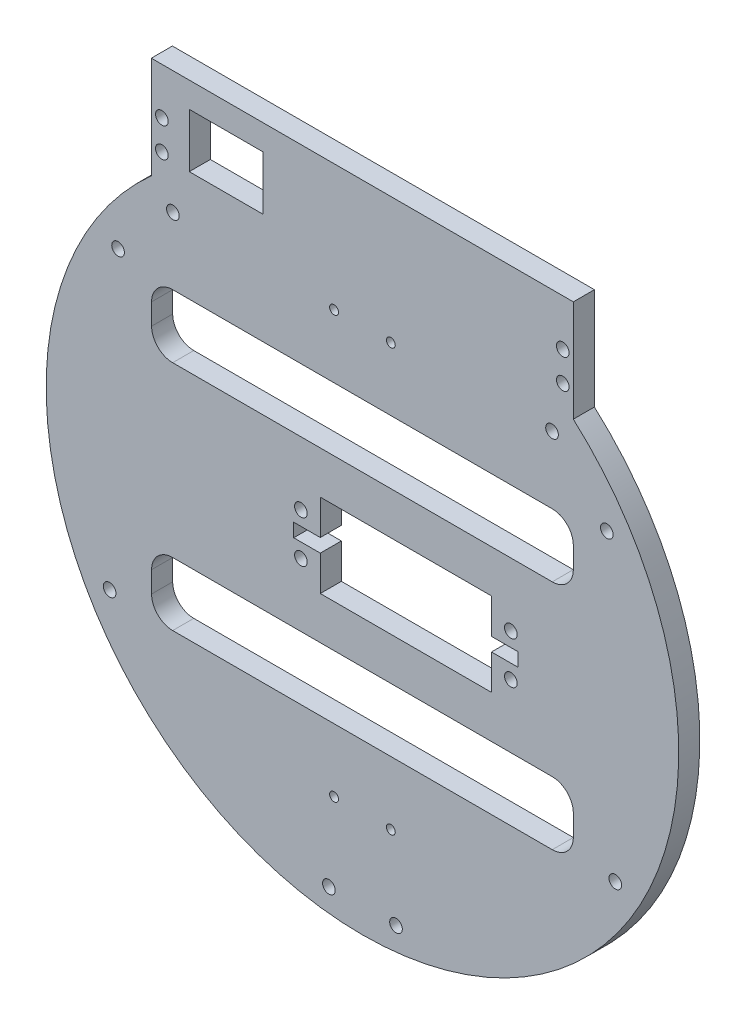
SolidWorks part; units mm, degrees
material "Acrílico (médio-alto impacto)"
ref_plane "Plano frontal" through (0, 0, 0) normal (0, 0, 1) x (1, 0, 0)
ref_plane "Plano superior" through (0, 0, 0) normal (0, 1, 0) x (1, 0, 0)
ref_plane "Plano direito" through (0, 0, 0) normal (1, 0, 0) x (0, 0, -1)
sketch "Esboço1" plane through (0, 0, 0) normal (0, 0, 1) x (1, 0, 0)
  line L0 (44.4954, -168.4305) -> (22.4463, -168.4305) construction
  line L1 (-33.4554, -168.4305) -> (-55.5046, -168.4305) construction
  line L2 (44.4954, -168.4305) -> (44.4954, -144.3322)
  line L3 (-55.5734, -168.3931) -> (-55.5734, -144.3322)
  line L4 (-55.5734, -144.3322) -> (44.4954, -144.3322)
  line L10 (-55.5046, -168.4305) -> (-55.5734, -168.3931)
  arc A0 (-55.5046, -168.4305) -> (44.4954, -168.4305) centre (-5.5046, -224.3322) ccw
  arc A1 (-33.4554, -168.4305) -> (22.4463, -168.4305) centre (-5.5046, -224.3322) ccw construction
  dimension "D1" = 150
  dimension "D2" = 125
  dimension "D3" = 80
extrude "Ressalto-extrusão1" add sketch "Esboço1" along normal blind 5 contours A0 L2 L4 L3 L10
sketch "Esboço2" plane through (0, 0, 5) normal (0, 0, 1) x (1, 0, 0)
  line L1 (-5.5046, -299.3322) -> (-5.5046, -271.3491) construction
  circle A0 centre (39.4463, -173.4305) radius 1.5
  circle A1 centre (52.4463, -187.4305) radius 1.5
  circle A2 centre (54.4463, -258.4305) radius 1.5
  circle A3 centre (-13.4554, -293.4305) radius 1.5
  circle A4 centre (2.4463, -293.4305) radius 1.5
  circle A5 centre (-65.4554, -258.4305) radius 1.5
  circle A8 centre (-63.4554, -187.4305) radius 1.5
  circle A9 centre (-50.4554, -173.4305) radius 1.5
  dimension "D3" = 3
  dimension "D6" = 3
  dimension "D9" = 3
  dimension "D12" = 3
extrude "Corte-extrusão1" cut sketch "Esboço2" against normal blind 10
sketch "Esboço3" plane through (0, 0, 5) normal (0, 0, 1) x (1, 0, 0)
  line L0 (-15.5046, -222.7322) -> (-15.5046, -214.4322)
  line L1 (-15.5046, -234.2322) -> (25.0954, -234.2322)
  line L2 (-15.5046, -234.2322) -> (-15.5046, -225.9322)
  line L3 (-15.5046, -214.4322) -> (25.0954, -214.4322)
  line L4 (25.0954, -234.2322) -> (25.0954, -214.4322)
  line L5 (25.0954, -225.9322) -> (31.3954, -225.9322)
  line L6 (25.0954, -225.9322) -> (25.0954, -222.7322)
  line L7 (25.0954, -222.7322) -> (31.3954, -222.7322)
  line L8 (31.3954, -225.9322) -> (31.3954, -222.7322)
  line L9 (-15.5046, -225.9322) -> (-21.8046, -225.9322)
  line L11 (-15.5046, -222.7322) -> (-21.8046, -222.7322)
  line L12 (-21.8046, -225.9322) -> (-21.8046, -222.7322)
  circle A0 centre (-5.5046, -224.3322) radius 5 construction
  circle A1 centre (29.6854, -229.3322) radius 1.5
  circle A2 centre (29.6854, -219.3322) radius 1.5
  circle A3 centre (-20.0946, -219.3322) radius 1.5
  circle A4 centre (-20.0946, -229.3322) radius 1.5
  point P19 (28.2454, -222.7322)
  dimension "D1" = 30.6
  dimension "D2" = 10
  dimension "D3" = 9.9
  dimension "D4" = 9.9
  dimension "D5" = 14.59
  dimension "D6" = 5
  dimension "D7" = 35.19
  dimension "D8" = 10
  dimension "D9" = 10
  dimension "D10" = 5
  dimension "D11" = 14.59
  dimension "D12" = 3
  dimension "D13" = 3
  dimension "D14" = 3
  dimension "D15" = 3
  dimension "D16" = 35.19
  dimension "D17" = 8.3
  dimension "D18" = 8.3
  dimension "D19" = 6.3
  dimension "D20" = 8.3
  dimension "D21" = 8.3
  dimension "D22" = 6.3
extrude "Corte-extrusão2" cut sketch "Esboço3" against normal blind 10 contours L5 L8 L7 L4 | L12 L9 L2 L1 L4 L3 L0 L11 | A1 | A2 | A4 | A3
sketch "Esboço4" plane through (0, 0, 5) normal (0, 0, 1) x (1, 0, 0)
  line L0 (-55.5734, -168.3931) -> (-55.5734, -144.3322) construction
  line L1 (-29.0734, -163.1322) -> (-46.5734, -163.1322)
  line L2 (-29.0734, -163.1322) -> (-29.0734, -150.3322)
  line L3 (-29.0734, -150.3322) -> (-46.5734, -150.3322)
  line L4 (-46.5734, -163.1322) -> (-46.5734, -150.3322)
  line L5 (-55.5734, -144.3322) -> (44.4954, -144.3322) construction
  point P6 (-55.5734, -156.3626)
  dimension "D1" = 17.5
  dimension "D2" = 12.8
  dimension "D3" = 9
  dimension "D4" = 6
extrude "Corte-extrusão3" cut sketch "Esboço4" against normal through all
sketch "Esboço5" plane through (0, 0, 0) normal (0, 0, -1) x (-1, 0, 0)
  line L0 (55.5734, -144.3322) -> (-44.4954, -144.3322) construction
  line L1 (55.5734, -168.3931) -> (55.5734, -144.3322) construction
  line L2 (-44.4954, -168.4305) -> (-44.4954, -144.3322) construction
  circle A0 centre (53.0734, -155.3322) radius 1.5
  circle A1 centre (53.0734, -162.3322) radius 1.5
  circle A2 centre (-41.9954, -155.3322) radius 1.5
  circle A3 centre (-41.9954, -162.3322) radius 1.5
  dimension "D1" = 11
  dimension "D2" = 18
  dimension "D3" = 2.5
  dimension "D4" = 2.5
  dimension "D5" = 3
  dimension "D6" = 3
  dimension "D7" = 11
  dimension "D8" = 18
  dimension "D9" = 2.5
  dimension "D10" = 3
  dimension "D11" = 3
  dimension "D12" = 2.5
extrude "Corte-extrusão4" cut sketch "Esboço5" against normal blind 10
sketch "Esboço6" plane through (0, 0, 0) normal (0, 0, -1) x (-1, 0, 0)
  line L0 (55.5734, -144.3322) -> (-44.4954, -144.3322) construction
  line L1 (80.5046, -224.3322) -> (64.1099, -224.3322) construction
  circle A0 centre (12.2346, -174.3322) radius 1.05
  circle A1 centre (-1.2254, -174.3322) radius 1.05
  circle A4 centre (-1.2254, -274.3322) radius 1.05
  circle A5 centre (12.2346, -274.3322) radius 1.05
  dimension "D1" = 13.46
  dimension "D2" = 2.1
  dimension "D3" = 2.1
  dimension "D4" = 43.27
  dimension "D5" = 43.27
  dimension "D6" = 30
extrude "Corte-extrusão5" cut sketch "Esboço6" against normal blind 10
sketch "Esboço7" plane through (0, 0, 0) normal (0, 0, -1) x (-1, 0, 0)
  line L1 (50.5046, -259.3322) -> (-39.4954, -259.3322)
  line L2 (55.5046, -254.3322) -> (55.5046, -249.3322)
  line L3 (50.5046, -244.3322) -> (-39.4954, -244.3322)
  line L4 (-44.4954, -254.3322) -> (-44.4954, -249.3322)
  line L5 (50.5046, -204.3322) -> (-39.4954, -204.3322)
  line L6 (55.5046, -199.3322) -> (55.5046, -194.3322)
  line L7 (50.5046, -189.3322) -> (-39.4954, -189.3322)
  line L8 (-44.4954, -199.3322) -> (-44.4954, -194.3322)
  arc A0 (-44.4954, -168.4305) -> (55.5046, -168.4305) centre (5.5046, -224.3322) ccw construction
  arc A1 (50.5046, -204.3322) -> (55.5046, -199.3322) centre (50.5046, -199.3322) ccw
  arc A2 (55.5046, -194.3322) -> (50.5046, -189.3322) centre (50.5046, -194.3322) ccw
  arc A3 (-39.4954, -189.3322) -> (-44.4954, -194.3322) centre (-39.4954, -194.3322) ccw
  arc A4 (-39.4954, -204.3322) -> (-44.4954, -199.3322) centre (-39.4954, -199.3322) cw
  arc A5 (-39.4954, -259.3322) -> (-44.4954, -254.3322) centre (-39.4954, -254.3322) cw
  arc A6 (-39.4954, -244.3322) -> (-44.4954, -249.3322) centre (-39.4954, -249.3322) ccw
  arc A7 (50.5046, -259.3322) -> (55.5046, -254.3322) centre (50.5046, -254.3322) ccw
  arc A8 (55.5046, -249.3322) -> (50.5046, -244.3322) centre (50.5046, -249.3322) ccw
  arc A9 (50.5046, -204.3322) -> (55.5046, -199.3322) centre (50.5046, -199.3322) ccw
  dimension "D9" = 5
  dimension "D10" = 5
  dimension "D1" = 15
  dimension "D2" = 15
  dimension "D3" = 40
  dimension "D4" = 35
  dimension "D5" = 50
  dimension "D6" = 50
  dimension "D7" = 50
  dimension "D8" = 50
extrude "Corte-extrusão6" cut sketch "Esboço7" against normal through all contours L2 A8 L3 A6 L4 A5 L1 A7 | A4 L5 A1 L6 A2 L7 A3 L8
